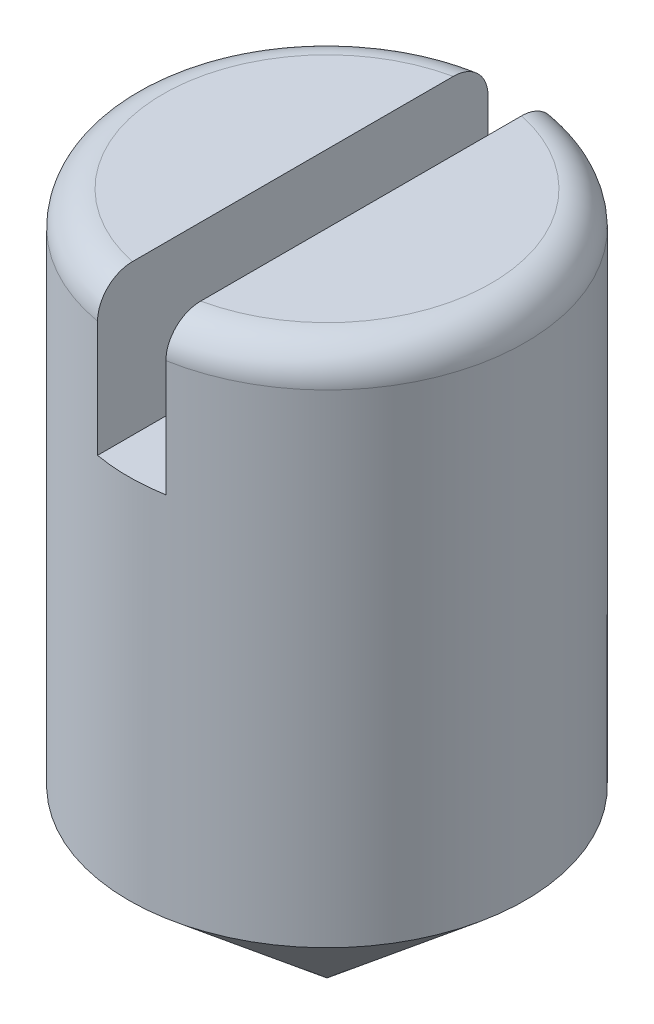
SolidWorks part; units mm, degrees
ref_plane "Plan de face" through (0, 0, 0) normal (0, 0, 1) x (1, 0, 0)
ref_plane "Plan de dessus" through (0, 0, 0) normal (0, 1, 0) x (1, 0, 0)
ref_plane "Plan de droite" through (0, 0, 0) normal (1, 0, 0) x (0, 0, -1)
sketch "Esquisse1" plane through (0, 0, 0) normal (0, 0, 1) x (1, 0, 0)
  line L0 (0, -16.3291) -> (0, 42.0235) construction
  line L1 (21.1318, 0) -> (-6.0034, 0) construction
  line L2 (-6.0034, 5) -> (21.1318, 5) construction
  line L3 (1.45, 17.2643) -> (1.45, -1.5144) construction
  line L4 (0, 0) -> (5.0984, 4.2781) construction
  line L5 (0, 5) -> (1.45, 5)
  line L6 (1.45, 5) -> (1.45, 1.2167)
  line L7 (1.45, 1.2167) -> (0, 0)
  line L8 (0, 0) -> (0, 5)
  dimension "D1" = 1.45
  dimension "D2" = 5
  dimension "D3" = 40
revolve "Révolution1" add sketch "Esquisse1" angle 360 about L0
ref_plane "Plan1" through (0, 0, 0) normal (0, 0, 1) x (1, 0, 0)
sketch "Esquisse2" plane through (0, 0, 0) normal (0, 0, 1) x (1, 0, 0)
  line L0 (0, 5.5805) -> (0, -0.5507) construction
  line L1 (0.25, 5.4538) -> (0.25, 3.4899) construction
  line L2 (-0.25, 5.4538) -> (-0.25, 3.4899) construction
  line L3 (1.9282, 5) -> (-0.5547, 5) construction
  line L4 (1.45, 5) -> (-1.45, 5) construction
  line L5 (1.9282, 3.9) -> (-0.656, 3.9) construction
  line L7 (-0.25, 5) -> (0.25, 5)
  line L8 (-0.25, 5) -> (-0.25, 3.9)
  line L9 (-0.25, 3.9) -> (0.25, 3.9)
  line L10 (0.25, 5) -> (0.25, 3.9)
  dimension "D1" = 1.1
  dimension "D2" = 0.5
  dimension "D3" = 0.25
extrude "Enlèv. mat.-Extru.1" cut sketch "Esquisse2" against normal mid plane 4
fillet "Congé1" radius 0.25 2 edges at (1.45, 5, 0) (-1.45, 5, 0)
